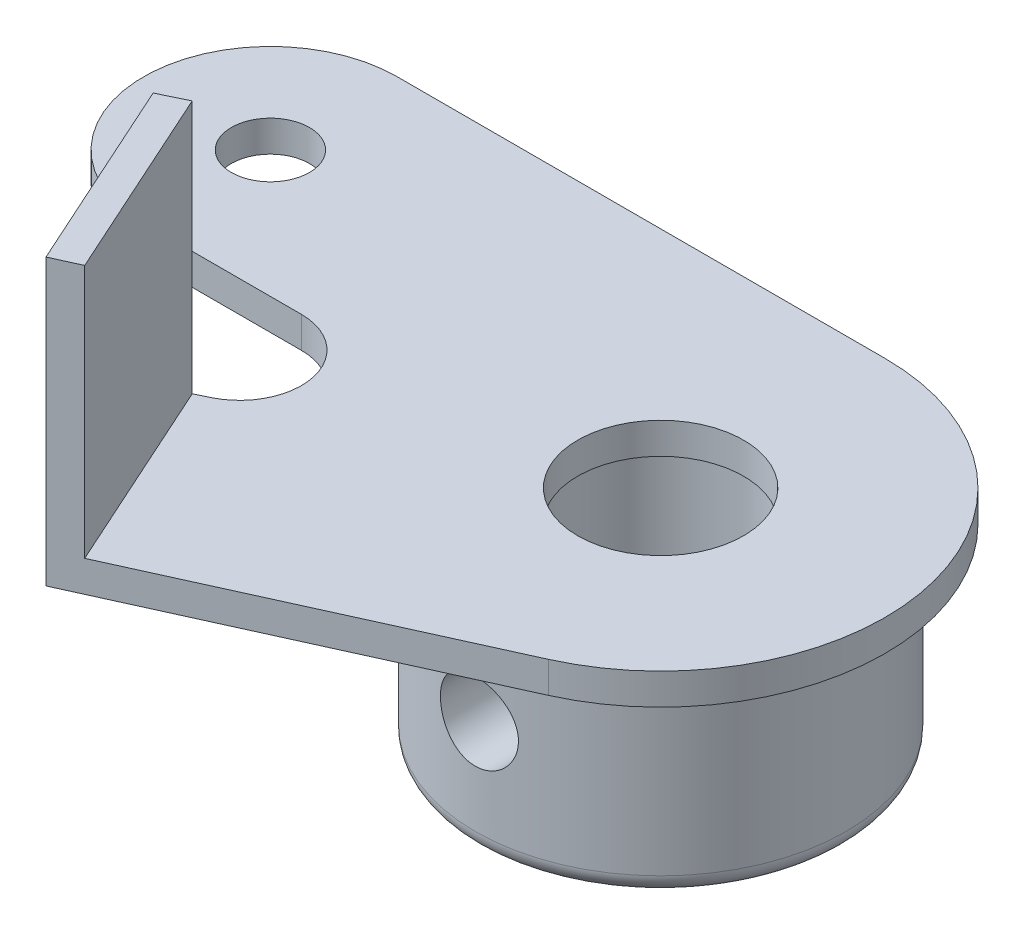
SolidWorks part; units mm, degrees
material "AISI 1020"
ref_plane "Plan de face" through (0, 0, 0) normal (0, 0, 1) x (1, 0, 0)
ref_plane "Plan de dessus" through (0, 0, 0) normal (0, 1, 0) x (1, 0, 0)
ref_plane "Plan de droite" through (0, 0, 0) normal (1, 0, 0) x (0, 0, -1)
sketch "Esquisse1" plane through (0, 0, 0) normal (0, 1, 0) x (1, 0, 0)
  line L0 (0, 11.5) -> (-25, 11.5)
  line L1 (-15.5325, -7.5102) -> (-17.5325, -8.4772)
  line L2 (-25, -1.5) -> (-16.9092, -1.5)
  line L3 (4.7385, -10.4784) -> (-13, -18.5)
  line L4 (-17.5325, -8.4772) -> (-13, -18.5)
  arc A0 (4.7385, -10.4784) -> (0, 11.5) centre (0, 0) ccw
  arc A1 (-25, 11.5) -> (-25, -1.5) centre (-25, 5) ccw
  arc A2 (-16.9092, -1.5) -> (-15.5325, -7.5102) centre (-16.9092, -4.6628) cw
  circle A3 centre (0, 0) radius 4.25
  circle A4 centre (-25, 5) radius 2
  point P10 (11.5, 0)
  point P11 (-31.5, 5)
  dimension "D1" = 23
  dimension "D2" = 6.5
  dimension "D8" = 8.5
  dimension "D9" = 4
  dimension "D3" = 43
  dimension "D4" = 13
  dimension "D5" = 30
  dimension "D6" = 2
extrude "Boss.-Extru.1" add sketch "Esquisse1" along normal blind 1.6
sketch "Esquisse2" plane through (0, 1.6, 0) normal (0, 1, 0) x (1, 0, 0)
  circle A0 centre (0, 0) radius 9.5
  circle A1 centre (0, 0) radius 4.5
  point P4 (0, 0)
  dimension "D1" = 19
extrude "Boss.-Extru.2" add sketch "Esquisse2" against normal blind 11.5
fillet "Congé1" radius 1 1 edges at (0, -9.9, 9.5)
sketch "Esquisse3" plane through (0, 1.6, 0) normal (0, 1, 0) x (1, 0, 0)
  line L0 (-17.5325, -8.4772) -> (-13, -18.5)
  line L1 (-13, -18.5) -> (-11.6337, -17.8821)
  line L2 (-16.182, -7.8242) -> (-11.6337, -17.8821)
  line L3 (-13, -18.5) -> (4.7385, -10.4784) construction
  line L4 (-15.5325, -7.5102) -> (-17.5325, -8.4772) construction
  line L5 (-16.182, -7.8242) -> (-17.5325, -8.4772)
  dimension "D1" = 1.5
extrude "Boss.-Extru.3" add sketch "Esquisse3" along normal blind 13
sketch "Esquisse4" plane through (0, 0, 0) normal (0, 0, 1) x (1, 0, 0)
  circle A0 centre (0, -4) radius 2
  dimension "D1" = 4
  dimension "D2" = 4
extrude "Enlèv. mat.-Extru.1" cut sketch "Esquisse4" along normal through all
